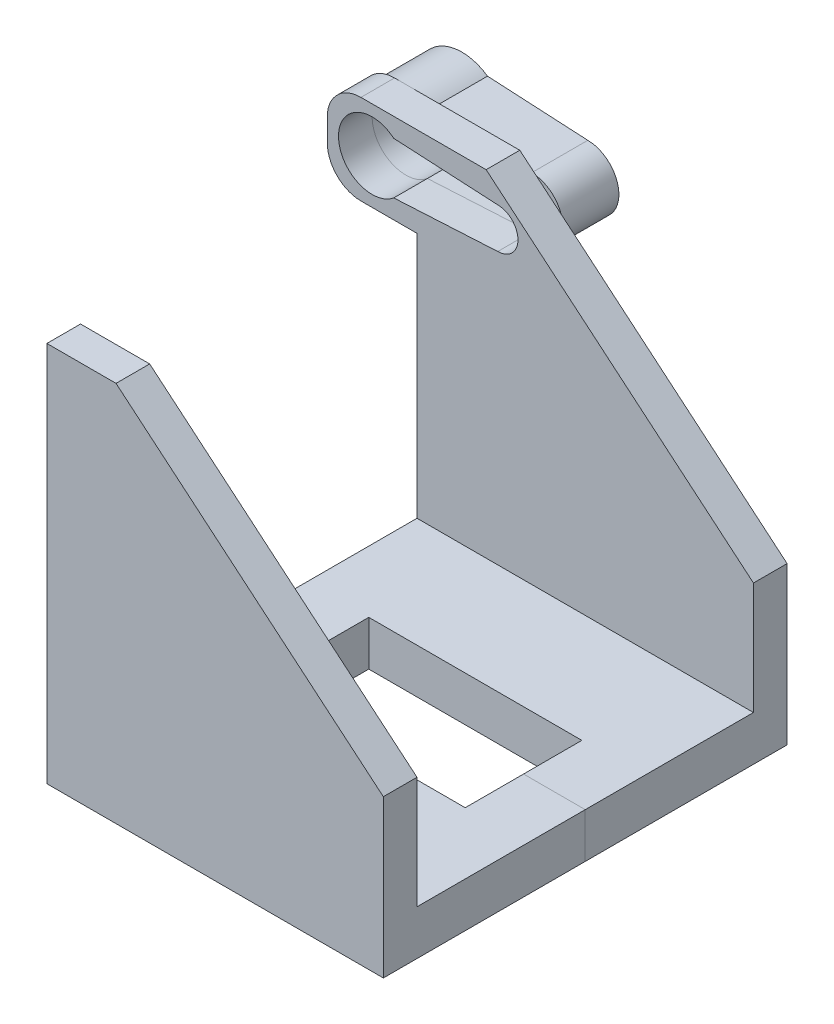
SolidWorks part; units mm, degrees
ref_plane "Front Plane" through (0, 0, 0) normal (0, 0, 1) x (1, 0, 0)
ref_plane "Top Plane" through (0, 0, 0) normal (0, 1, 0) x (1, 0, 0)
ref_plane "Right Plane" through (0, 0, 0) normal (1, 0, 0) x (0, 0, -1)
sketch "Sketch1" plane through (0, 0, 0) normal (0, 1, 0) x (1, 0, 0)
  line L0 (-19.05, 0) -> (19.05, 0) construction
  line L1 (-19.05, -22.86) -> (19.05, -22.86)
  line L2 (-19.05, -22.86) -> (-19.05, 22.86)
  line L3 (-19.05, 22.86) -> (19.05, 22.86)
  line L4 (19.05, -22.86) -> (19.05, 22.86)
  line L5 (0, 22.86) -> (0, -22.86) construction
  line L11 (-12.065, 6.604) -> (12.065, 6.604)
  line L12 (-12.065, 6.604) -> (-12.065, -6.604)
  line L21 (-12.065, -6.604) -> (12.065, -6.604)
  line L22 (12.065, 6.604) -> (12.065, -6.604)
  line L23 (-12.065, 6.604) -> (12.065, -6.604) construction
  line L24 (-12.065, -6.604) -> (12.065, 6.604) construction
  point P0 (1.7214, 0.9878)
  point P6 (0, 0)
  dimension "D2" = 24.13
  dimension "D3" = 38.1
  dimension "D4" = 45.72
  dimension "0.52" = 13.208
extrude "Boss-Extrude1" add sketch "Sketch1" along normal blind 5.08
sketch "Sketch2" plane through (0, 5.08, 0) normal (0, 1, 0) x (1, 0, 0)
  line L0 (19.05, -22.86) -> (19.05, 22.86) construction
  line L1 (-19.05, 22.86) -> (19.05, 22.86)
  line L2 (-19.05, 22.86) -> (-19.05, 19.05)
  line L3 (-19.05, 19.05) -> (19.05, 19.05)
  line L4 (19.05, 22.86) -> (19.05, 19.05)
  line L6 (-19.05, -22.86) -> (19.05, -22.86)
  line L7 (-19.05, -22.86) -> (-19.05, -19.05)
  line L8 (-19.05, -19.05) -> (19.05, -19.05)
  line L9 (19.05, -22.86) -> (19.05, -19.05)
  dimension "D1" = 3.81
extrude "Boss-Extrude2" add sketch "Sketch2" along normal blind 38.1
chamfer "Chamfer1" distance 25.4 angle 50 2 edges at (19.05, 43.18, 20.955) (19.05, 43.18, -20.955)
sketch "Sketch3" plane through (-19.05, 0, 0) normal (-1, 0, 0) x (0, 0, 1)
  line L0 (-19.05, 43.18) -> (-19.05, 5.08) construction
  line L1 (-22.86, 43.18) -> (-19.05, 43.18)
  line L2 (-22.86, 43.18) -> (-22.86, 33.02)
  line L3 (-22.86, 33.02) -> (-19.05, 33.02)
  line L4 (-19.05, 43.18) -> (-19.05, 33.02)
  dimension "D1" = 10.16
extrude "Boss-Extrude3" add sketch "Sketch3" along normal blind 10.16
fillet "Fillet1" radius 3.81 2 edges at (-29.21, 33.02, -20.955) (-29.21, 43.18, -20.955)
sketch "Sketch4" plane through (0, 0, -22.86) normal (0, 0, -1) x (-1, 0, 0)
  line L0 (24.13, 38.1) -> (7.62, 38.1) construction
  line L1 (29.21, 39.37) -> (29.21, 36.83) construction
  line L2 (21.6838, 35.179) -> (21.6838, 41.021) construction
  line L4 (24.13, 38.1) -> (29.21, 38.1) construction
  line L6 (9.906, 40.386) -> (21.6838, 41.021)
  line L7 (9.906, 35.814) -> (21.6838, 35.179)
  arc A0 (21.6838, 35.179) -> (21.6838, 41.021) centre (24.13, 38.1) ccw
  arc A2 (9.906, 40.386) -> (9.906, 35.814) centre (9.906, 38.1) ccw
  dimension "D1" = 7.62
  dimension "D4" = 4.572
  dimension "D2" = 5.08
  dimension "D3" = 16.51
  dimension "D5" = 5.842
extrude "Extrude-Thin2" add sketch "Sketch4" along normal blind 6.35 thin thin type one direction wall 1.27
sketch "Sketch6" plane through (0, 0, -22.86) normal (0, 0, -1) x (-1, 0, 0)
  line L0 (24.13, 38.1) -> (7.62, 38.1) construction
  line L1 (21.6838, 35.179) -> (21.6838, 41.021) construction
  line L2 (24.13, 38.1) -> (29.21, 38.1) construction
  line L3 (9.906, 40.386) -> (21.6838, 41.021)
  line L4 (9.906, 35.814) -> (21.6838, 35.179)
  arc A0 (21.6838, 35.179) -> (21.6838, 41.021) centre (24.13, 38.1) ccw
  arc A1 (9.906, 40.386) -> (9.906, 35.814) centre (9.906, 38.1) ccw
  dimension "D1" = 7.62
  dimension "D4" = 4.572
  dimension "D2" = 5.08
  dimension "D3" = 16.51
  dimension "D5" = 5.842
extrude "Cut-Extrude3" cut sketch "Sketch6" against normal up to next (3.81 mm away)
split "Split1" trim tools "Front Plane" bodies to split 110 resulting bodies 114 115
